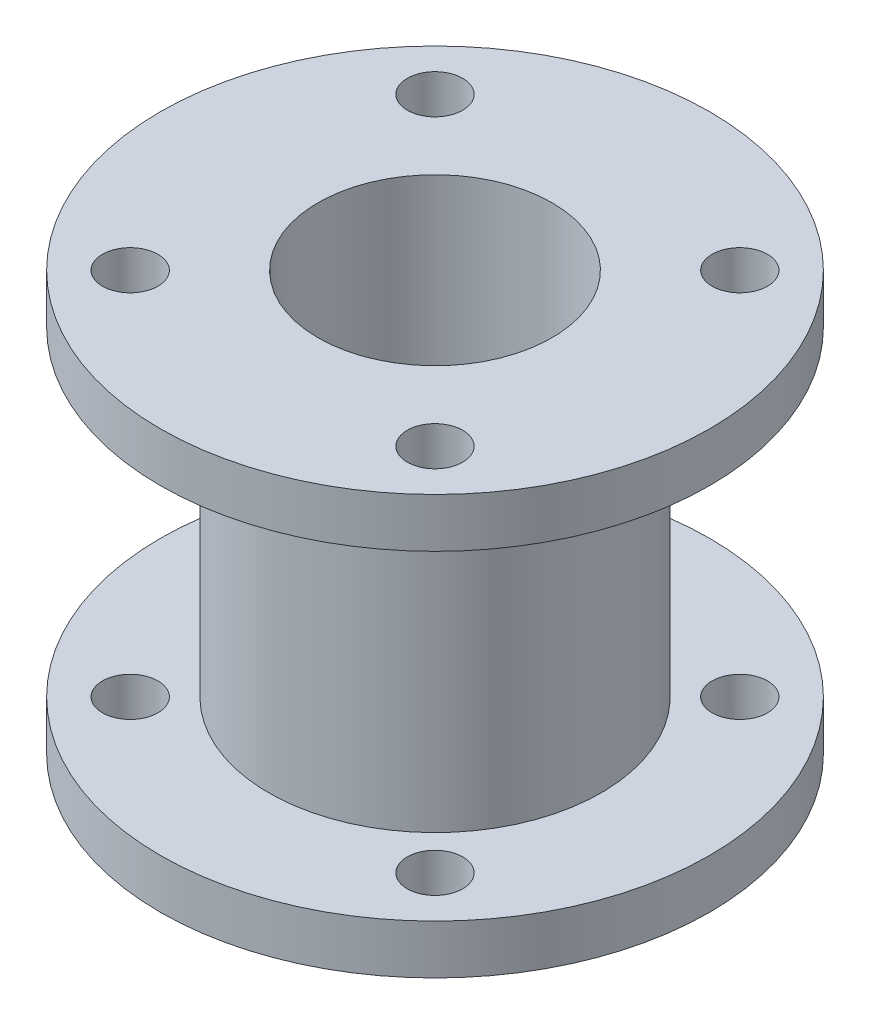
SolidWorks part; units mm, degrees
ref_plane "Front Plane" through (0, 0, 0) normal (0, 0, 1) x (1, 0, 0)
ref_plane "Top Plane" through (0, 0, 0) normal (0, 1, 0) x (1, 0, 0)
ref_plane "Right Plane" through (0, 0, 0) normal (1, 0, 0) x (0, 0, -1)
sketch "Sketch1" plane through (0, 0, 0) normal (0, 0, 1) x (1, 0, 0)
  line L0 (0, 0) -> (0, 69.1324) construction
  line L1 (13.5, 26) -> (22.3, 26)
  line L2 (9.5, 30) -> (9.5, -4)
  line L3 (13.5, 26) -> (13.5, 0)
  line L4 (9.5, 30) -> (22.3, 30)
  line L5 (22.3, 26) -> (22.3, 30)
  line L6 (13.5, 0) -> (22.3, 0)
  line L7 (22.3, 0) -> (22.3, -4)
  line L8 (22.3, -4) -> (9.5, -4)
  line L9 (9.5, 30) -> (9.5, 0) construction
  dimension "D2" = 4
  dimension "D3" = 26
  dimension "D4" = 44.6
  dimension "D1" = 13.5
revolve "Revolve1" add sketch "Sketch1" angle 360 about L0
hole_wizard "M4 Clearance Hole1" positions "Sketch3" profile "Sketch2" hole size "M4" standard "ISO" end condition through all
sketch "Sketch3" plane through (0, -4, 0) normal (0, -1, 0) x (1, 0, 0)
  line L1 (-12.3744, -12.3744) -> (12.3744, -12.3744) construction
  line L2 (-12.3744, -12.3744) -> (-12.3744, 12.3744) construction
  line L3 (-12.3744, 12.3744) -> (12.3744, 12.3744) construction
  line L4 (12.3744, -12.3744) -> (12.3744, 12.3744) construction
  line L5 (-12.3744, -12.3744) -> (12.3744, 12.3744) construction
  line L6 (-12.3744, 12.3744) -> (12.3744, -12.3744) construction
  point P0 (-12.3744, 12.3744)
  point P220 (12.3744, 12.3744)
  point P222 (12.3744, -12.3744)
  point P224 (-12.3744, -12.3744)
  dimension "D1" = 35
  dimension "D2" = 35
sketch "Sketch2" plane through (-12.3744, -4, 12.3744) normal (1, 0, 0) x (0, 0, -1)
  line L0 (0, 0) -> (0, 34)
  line L1 (0, 34) -> (2.25, 34)
  line L2 (2.25, 34) -> (2.25, 0)
  line L5 (2.25, 0) -> (0, 0)
  line L11 (0, -6.35) -> (0, 107.95) construction
  dimension "Thru Hole Dia." = 4.5
  dimension "Thru Hole Depth" = 34
